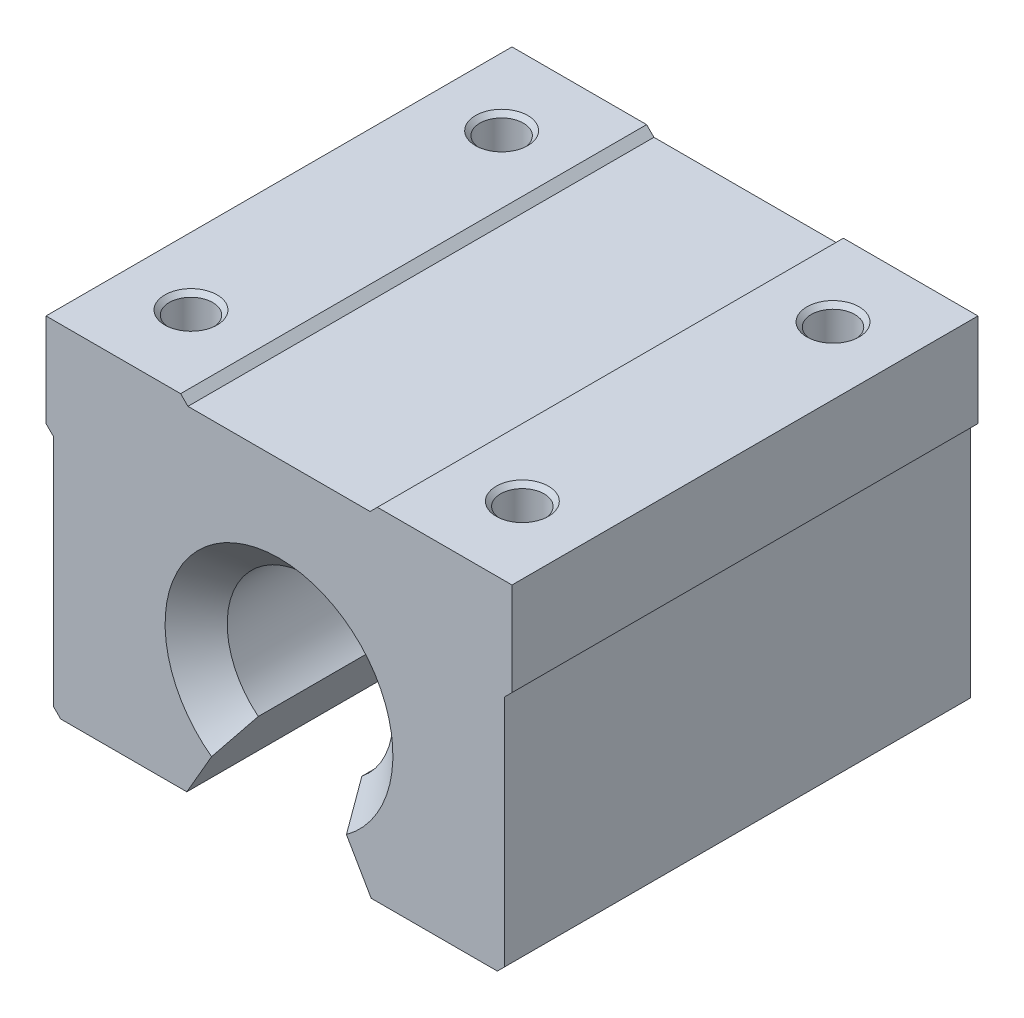
SolidWorks part; units mm, degrees
ref_plane "Front Plane" through (0, 0, 0) normal (0, 0, 1) x (1, 0, 0)
ref_plane "Top Plane" through (0, 0, 0) normal (0, 1, 0) x (1, 0, 0)
ref_plane "Right Plane" through (0, 0, 0) normal (1, 0, 0) x (0, 0, -1)
sketch "Sketch1" plane through (0, 0, 0) normal (0, 0, 1) x (1, 0, 0)
  line L0 (-22.5, 20) -> (-22.5, 11)
  line L5 (-22.5, 11) -> (-21.7929, 10.2929)
  line L6 (-21.7929, 10.2929) -> (-21.7929, -12.2929)
  line L7 (-21.7929, -12.2929) -> (-21.0858, -13)
  line L8 (-21.0858, -13) -> (-8.9, -13)
  line L9 (-8.9, -13) -> (-5, -6.245)
  line L10 (-22.5, 20) -> (-9.5, 20)
  line L11 (-9.5, 20) -> (-8.7929, 19.2929)
  line L12 (-8.7929, 19.2929) -> (8.7929, 19.2929)
  line L13 (0, 0) -> (0, 19.2929) construction
  line L14 (8.9, -13) -> (5, -6.245)
  line L15 (21.0858, -13) -> (8.9, -13)
  line L16 (21.7929, -12.2929) -> (21.0858, -13)
  line L17 (21.7929, 10.2929) -> (21.7929, -12.2929)
  line L18 (22.5, 11) -> (21.7929, 10.2929)
  line L19 (22.5, 20) -> (22.5, 11)
  line L20 (22.5, 20) -> (9.5, 20)
  line L21 (9.5, 20) -> (8.7929, 19.2929)
  arc A0 (5, -6.245) -> (-5, -6.245) centre (0, 0) ccw
  dimension "D2" = 16
  dimension "D1" = 45
  dimension "D3" = 33
  dimension "D4" = 60
  dimension "D5" = 135
  dimension "D6" = 9
  dimension "D7" = 10
  dimension "D8" = 1
  dimension "D9" = 20
  dimension "D10" = 13
extrude "Boss-Extrude1" add sketch "Sketch1" along normal mid plane 45
sketch "Sketch2" plane through (0, 20, 0) normal (0, 1, 0) x (1, 0, 0)
  line L1 (-16, -15) -> (16, -15) construction
  line L2 (-16, -15) -> (-16, 15) construction
  line L3 (-16, 15) -> (16, 15) construction
  line L4 (16, -15) -> (16, 15) construction
  line L5 (-16, -15) -> (16, 15) construction
  line L6 (-16, 15) -> (16, -15) construction
  point P0 (0, 0)
  point P7 (-16, 15)
  point P8 (-16, -15)
  point P9 (16, -15)
  point P10 (16, 15)
  dimension "D1" = 32
  dimension "D2" = 30
hole_wizard "M5x0.8 Tapped Hole1" positions "3DSketch1" profile "Sketch3" tap size "M5x0.8" standard "ANSI Metric"
sketch3d "3DSketch1"
  point P0 (16, 20, 15)
  point P3 (16, 20, -15)
  point P6 (-16, 20, -15)
  point P9 (-16, 20, 15)
sketch "Sketch3" plane through (16, 20, 15) normal (1, 0, 0) x (0, 0, 1)
  line L0 (0, 0) -> (0, 13.2618)
  line L1 (0, 13.2618) -> (2.1, 12)
  line L2 (2.1, 12) -> (2.1, 0.425)
  line L3 (2.1, 0.425) -> (2.525, 0)
  line L5 (2.525, 0) -> (0, 0)
  line L6 (-2.1, 0.425) -> (-2.525, 0) construction
  line L10 (0, 13.2618) -> (-2.1, 12) construction
  line L11 (0, -6.35) -> (0, 107.95) construction
  dimension "Tap Drill Dia." = 4.2
  dimension "Tap Drill Depth" = 12
  dimension "Near C'Sink Dia." = 5.05
  dimension "Near C'Sink Angle" = 90
  dimension "Drill Angle" = 118
cosmetic thread "Hole Thread1" parameters "D1"=9.906, "D2"=5
cosmetic thread "Hole Thread2" parameters "D1"=9.906, "D2"=5
cosmetic thread "Hole Thread3" parameters "D1"=9.906, "D2"=5
cosmetic thread "Hole Thread4" parameters "D1"=9.906, "D2"=5
chamfer "Chamfer1" distance 3 angle 45 2 edges at (0, 8, -22.5) (0, 8, 22.5)
